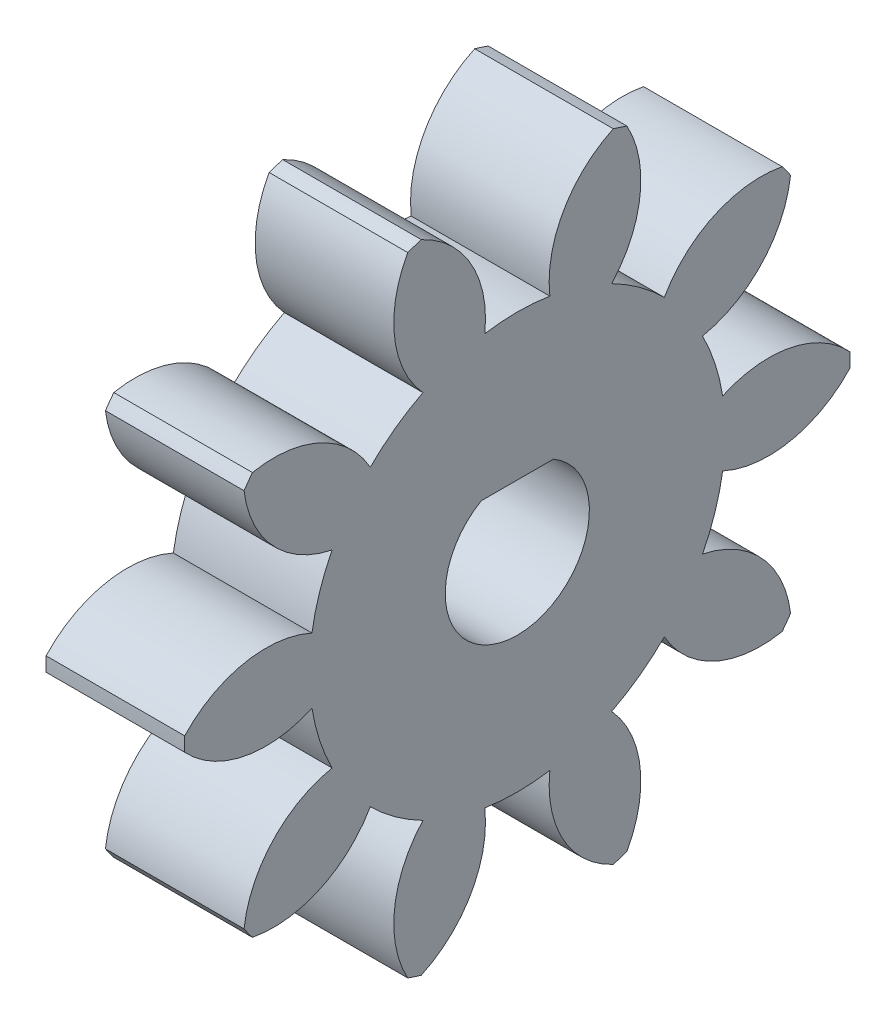
SolidWorks part; units mm, degrees
ref_plane "Plane1" through (0, 0, 0) normal (0, 0, 1) x (1, 0, 0)
ref_plane "Plane2" through (0, 0, 0) normal (0, 1, 0) x (1, 0, 0)
ref_plane "Plane3" through (0, 0, 0) normal (1, 0, 0) x (0, 0, -1)
other "Configuration Table"
sketch "HoldingSke" plane through (0, 0, 0) normal (0, 1, 0) x (1, 0, 0)
  line L0 (0, 0) -> (0.4924, -0.0868)
  line L1 (-15, 0) -> (100, 0) construction
  line L2 (0, 0) -> (-2.1039, 2.3779)
  line L3 (0, 0) -> (-11.863, 4.5341)
  line L4 (0, 0) -> (8.5048, 1.4996)
  line L5 (0, 0) -> (-46.8476, -17.4728)
  line L6 (0, 0) -> (-4.1448, -2.7965)
  line L7 (-2.1039, 2.3779) -> (8.6586, 51.2059)
  line L8 (-76.2, 54.61) -> (-76.1, 54.61)
  line L9 (-71.009, 38.7566) -> (-53.1078, 45.2721)
  line L10 (-76.2, 71.12) -> (104.1128, 71.12)
  line L11 (0, 0) -> (-5, 0)
  line L12 (-76.2, 101.6) -> (-76.133, 101.6)
  line L13 (24.9733, 27.94) -> (52.9518, 28.4284)
  line L14 (24.9733, 27.94) -> (24.9743, 27.94)
  line L15 (24.9733, 27.94) -> (100.4006, 29.5858)
  line L16 (-63.627, -2) -> (-12.827, -2)
  circle A0 centre (0, 0) radius 0.5
  circle A1 centre (0, 0) radius 7.499
  circle A2 centre (0, 0) radius 37.5
  circle A3 centre (0, 0) radius 0.5
  dimension "MHD" = 14.998
  dimension "Hub_dia" = 75
  dimension "Bore" = 1
  dimension "MBD" = 1
  dimension "Num_teeth" = 10
  dimension "Pitch" = 0.5
  dimension "Overall_len" = 50
  dimension "Show_teeth" = 10
  dimension "Thickness" = 5
  dimension "OAL" = 50.0001
  dimension "T_dim" = 0.1
  dimension "Ap" = 20
  dimension "H" = 19.05
  dimension "Pitch_radius" = 180.3128
  dimension "Width" = 5
  dimension "Backlash" = 0.067
  dimension "Addendum_fac" = 1
  dimension "Dedendum_fac" = 1.25
  dimension "Clearance_fac" = 0.25
  dimension "Dedendum_add" = 0.001
  dimension "Module" = 2
sketch "BasProSke" plane through (0, 0, 0) normal (0, 1, 0) x (1, 0, 0)
  line L0 (-10, 0) -> (60, 0) construction
  line L1 (0, 0) -> (0, 12)
  line L2 (0, 0) -> (5, 0)
  line L3 (5, 0) -> (5, 12)
  line L4 (5, 12) -> (0, 12)
  dimension "Thickness" = 5
  dimension "Diameter" = 24
revolve "Base-Revolve" add sketch "BasProSke" angle 360 about L0
sketch "TooCutSke" plane through (0, 0, 0) normal (1, 0, 0) x (0, 0, -1)
  line L1 (0, 0) -> (0, 107) construction
  line L2 (0, 0) -> (-1.6814, 9.8576) construction
  line L3 (0, 0) -> (-6.1153, 18.8209) construction
  line L4 (-1.6814, 9.8576) -> (-3.0576, 9.4105) construction
  arc A0 (1.1737, 7.4066) -> (-1.1737, 7.4066) centre (0, 0) ccw
  arc A1 (3.4979, 11.5054) -> (-3.4979, 11.5054) centre (0, 0) ccw
  circle A2 centre (0, 0) radius 10 construction
  circle A3 centre (0, 0) radius 9.3969 construction
  arc A4 (-1.1737, 7.4066) -> (-3.4979, 11.5054) centre (-5.1477, 7.8615) ccw
  arc A5 (3.4979, 11.5054) -> (1.1737, 7.4066) centre (5.1477, 7.8615) ccw
  dimension "Root_dia" = 14.998
  dimension "Overcut_dia" = 24.0508
  dimension "Pitch_dia" = 20
  dimension "Base_dia" = 18.7939
  dimension "Flank_rad" = 4
  dimension "Half_ang" = 18
  dimension "Half_CT" = 1.4471
extrude "ToothCut" cut sketch "TooCutSke" along normal through all
fillet "Breaks" [suppressed] radius 0.04
fillet "RootFillets" [suppressed] radius 0.501
pattern_circular "TeethCuts" count 10 every 36 about axis through (-10, 0, 0) along (1, 0, 0) of "ToothCut", "RootFillets", "Breaks"
sketch "HubNeaOneSke" plane through (0, 0, 0) normal (-1, 0, 0) x (0, 0, 1)
  circle A0 centre (0, 0) radius 7.499
  dimension "Diameter" = 14.998
extrude "HubNearOne" [suppressed] add sketch "HubNeaOneSke" along normal blind 45.0001
sketch "HubNeaBotSke" plane through (0, 0, 0) normal (-1, 0, 0) x (0, 0, 1)
  circle A0 centre (0, 0) radius 7.499
  dimension "Diameter" = 14.998
extrude "HubNearBoth" [suppressed] add sketch "HubNeaBotSke" along normal blind 22.5
ref_plane "FarPln" through (5, 0, 0) normal (1, 0, 0) x (0, 0, -1)
sketch "HubFarSke" plane through (5, 0, 0) normal (1, 0, 0) x (0, 0, -1)
  circle A0 centre (0, 0) radius 7.499
  dimension "Diameter" = 14.998
extrude "HubFar" [suppressed] add sketch "HubFarSke" along normal blind 22.5
sketch "BorSke" plane through (0, 0, 0) normal (1, 0, 0) x (0, 0, -1)
  circle A0 centre (0, 0) radius 0.5
  dimension "Diameter" = 1
extrude "Bore" cut sketch "BorSke" along normal mid plane 100.0001
sketch "KeySke" plane through (0, 0, 0) normal (1, 0, 0) x (0, 0, -1)
  line L0 (-0.05, 0) -> (-0.05, 0.6)
  line L1 (-0.05, 0.6) -> (0.05, 0.6)
  line L2 (0.05, 0.6) -> (0.05, 0)
  line L3 (0, 0) -> (0, 34) construction
  line L4 (-0.05, 0) -> (0.05, 0)
  dimension "Offset" = 0.6
  dimension "Width" = 0.1
extrude "Keyway" [suppressed] cut sketch "KeySke" along normal mid plane 100.0001
pattern_circular "Keyway2" [suppressed] count 2 every 90 about axis through (-10, 0, 0) along (1, 0, 0)
sketch "Sketch2" plane through (0, 0, 0) normal (-1, 0, 0) x (0, 0, 1)
  line L0 (0, 2.25) -> (0, -2.25) construction
  line L1 (-1.3029, 2.25) -> (1.3029, 2.25)
  circle A0 centre (0, 0) radius 2.6
  point P6 (0, 0)
  point P9 (0, 2.25)
extrude "Cut-Extrude1" cut sketch "Sketch2" against normal blind 10
equation "' \"Module@HoldingSke\" = 6.35"
equation "' \"Num_teeth@HoldingSke\" = 12"
equation "' \"Ap@HoldingSke\" =  20"
equation "' \"Ap@HoldingSke\" = 20"
equation "' \"Width@HoldingSke\" = 0.5 * 25.4"
equation "' \"Hub_dia@HoldingSke\"= 1 * 25.4"
equation "' \"Hub_dia@HoldingSke\" = 1 * 25.4"
equation "' \"Overall_len@HoldingSke\" = 1.0 * 25.4"
equation "' \"Bore@HoldingSke\" = 0.75 * 25.4"
equation "' \"T_dim@HoldingSke\" = 0.1 * 25.4"
equation "' \"Width@KeySke\" = 0.25 * 25.4"
equation "' \"Show_teeth@HoldingSke\" = 13"
equation "' \"Backlash@HoldingSke\" = 0.009 * 25.4"
equation "' \"Addendum_fac@HoldingSke\" = 1.0"
equation "' \"Dedendum_fac@HoldingSke\" = 1.25"
equation "' \"Dedendum_add@HoldingSke\" = 0.00005 * 25.4"
equation "' \"Clearance_fac@HoldingSke\" = 0.25"
equation "\"Pitch@HoldingSke\" = 1 / \"Module@HoldingSke\""
equation "\"Overcut_dia@TooCutSke\" = (\"Num_teeth@HoldingSke\" + 2 * \"Addendum_fac@HoldingSke\") / \"Pitch@HoldingSke\" + 0.002 * 25.4"
equation "\"Pitch_dia@TooCutSke\" = \"Num_teeth@HoldingSke\" / \"Pitch@HoldingSke\""
equation "\"Base_dia@TooCutSke\" = \"Num_teeth@HoldingSke\" / \"Pitch@HoldingSke\" * cos((\"Ap@HoldingSke\"  * 3.14159265 / 180))"
equation "\"Root_dia@TooCutSke\" = (\"Num_teeth@HoldingSke\" + 2) / \"Pitch@HoldingSke\" - 2 * (\"Addendum_fac@HoldingSke\" + \"Dedendum_fac@HoldingSke\") / \"Pitch@HoldingSke\" - \"Dedendum_add@HoldingSke\" * 2"
equation "\"Half_ang@TooCutSke\" = 180 / \"Num_teeth@HoldingSke\""
equation "\"Half_CT@TooCutSke\" = \"Num_teeth@HoldingSke\" / \"Pitch@HoldingSke\" * sin((3.14159265 / 2 / \"Num_teeth@HoldingSke\")) / 2 - 7 * \"Backlash@HoldingSke\" / 4"
equation "\"Flank_rad@TooCutSke\" = \"Num_teeth@HoldingSke\" / \"Pitch@HoldingSke\" / 5"
equation "\"Radius@RootFillets\" = \"Clearance_fac@HoldingSke\" / \"Pitch@HoldingSke\" + \"Dedendum_add@HoldingSke\""
equation "\"Break_rad@Breaks\" = 0.02 / \"Pitch@HoldingSke\""
equation "\"Thickness@HoldingSke\" = \"Width@HoldingSke\""
equation "\"OAL@HoldingSke\" = \"Thickness@HoldingSke\""
equation "\"MHD@HoldingSke\" = (\"Num_teeth@HoldingSke\" + 2) / \"Pitch@HoldingSke\" - 2 * (\"Addendum_fac@HoldingSke\" + \"Dedendum_fac@HoldingSke\")  / \"Pitch@HoldingSke\" - \"Dedendum_add@HoldingSke\" * 2"
equation "\"MBD@HoldingSke\" = (\"Num_teeth@HoldingSke\" + 2) / \"Pitch@HoldingSke\" - 2 * (\"Addendum_fac@HoldingSke\" + \"Dedendum_fac@HoldingSke\")  / \"Pitch@HoldingSke\" - \"Dedendum_add@HoldingSke\" * 2 - 0.002 * 25.4"
equation "\"MHD@HoldingSke\" = ((sgn( \"MHD@HoldingSke\" - \"Hub_dia@HoldingSke\" )-1)*( \"MHD@HoldingSke\" - \"Hub_dia@HoldingSke\" ))/-2+ \"Hub_dia@HoldingSke\""
equation "\"MBD@HoldingSke\" = ((sgn( \"MBD@HoldingSke\" - \"Bore@HoldingSke\" )-1)*( \"MBD@HoldingSke\" - \"Bore@HoldingSke\" ))/-2+ \"Bore@HoldingSke\""
equation "\"OAL@HoldingSke\" = ((sgn( \"OAL@HoldingSke\" - \"Overall_len@HoldingSke\" )+1)*( \"OAL@HoldingSke\" - \"Overall_len@HoldingSke\" ))/2 + \"Overall_len@HoldingSke\" + 0.000002 * 25.4"
equation "\"Num_teeth@TeethCuts\" = int( \"Show_teeth@HoldingSke\" ) + 1"
equation "\"Num_teeth@TeethCuts\" = ((sgn( \"Num_teeth@TeethCuts\" - \"Num_teeth@HoldingSke\" )-1)*( \"Num_teeth@TeethCuts\" - \"Num_teeth@HoldingSke\" ))/-2+ \"Num_teeth@HoldingSke\""
equation "\"Num_teeth@TeethCuts\" = ((sgn( \"Num_teeth@TeethCuts\" - 2.0)+1)*( \"Num_teeth@TeethCuts\" - 2.0))/2 +2.0"
equation "\"Angle@TeethCuts\" = 360.0 / \"Num_teeth@HoldingSke\""
equation "\"Diameter@BasProSke\" = (\"Num_teeth@HoldingSke\" + 2 * \"Addendum_fac@HoldingSke\") / \"Pitch@HoldingSke\""
equation "\"Thickness@BasProSke\"  = \"Thickness@HoldingSke\""
equation "' \"Fillet_rad@BasProSke\" =  \"Thickness@HoldingSke\" * 0.05"
equation "' \"Fillet_rad@BasProSke\" = \"Thickness@HoldingSke\" * 0.05"
equation "\"MHD@HoldingSke\" = ((sgn( \"MHD@HoldingSke\" - \"Root_dia@TooCutSke\" )-1)*( \"MHD@HoldingSke\" - \"Root_dia@TooCutSke\" ))/-2+ \"Root_dia@TooCutSke\""
equation "\"Diameter@HubNeaOneSke\" = \"MHD@HoldingSke\""
equation "\"Length@HubNearOne\" = \"OAL@HoldingSke\" - \"Thickness@BasProSke\""
equation "\"Diameter@HubNeaBotSke\" = \"MHD@HoldingSke\""
equation "\"Length@HubNearBoth\" = ( \"OAL@HoldingSke\" - \"Thickness@BasProSke\" ) / 2.0"
equation "\"Thickness@FarPln\" = \"Thickness@BasProSke\""
equation "\"Diameter@HubFarSke\" = \"MHD@HoldingSke\""
equation "\"Length@HubFar\" = ( \"OAL@HoldingSke\" - \"Thickness@BasProSke\" ) / 2.0"
equation "\"Diameter@BorSke\" = \"MBD@HoldingSke\""
equation "\"D1@Bore\" = \"OAL@HoldingSke\" * 2.0"
equation "\"D1@Keyway\" = \"OAL@HoldingSke\" * 2.0"
equation "\"Offset@KeySke\" = \"T_dim@HoldingSke\" + \"MBD@HoldingSke\" / 2.0"
